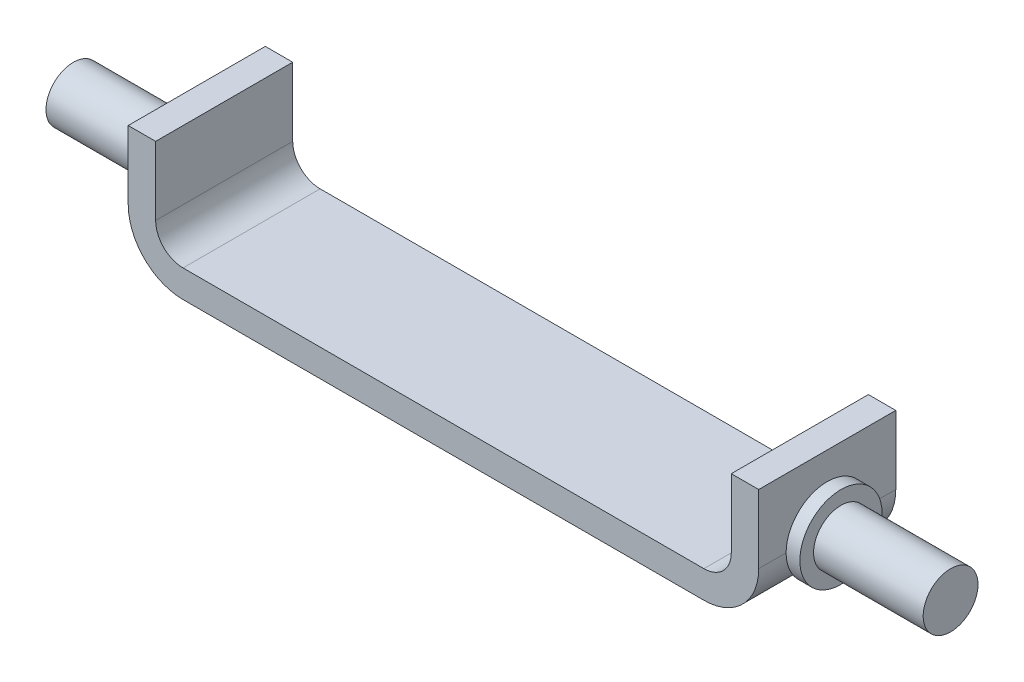
SolidWorks part; units mm, degrees
ref_plane "Front Plane" through (0, 0, 0) normal (0, 0, 1) x (1, 0, 0)
ref_plane "Top Plane" through (0, 0, 0) normal (0, 1, 0) x (1, 0, 0)
ref_plane "Right Plane" through (0, 0, 0) normal (1, 0, 0) x (0, 0, -1)
sketch "Sketch1" plane through (0, 0, 0) normal (0, 0, 1) x (1, 0, 0)
  line L0 (-96.4179, 0) -> (93.5821, 0)
  line L1 (-106.4179, 10) -> (-106.4179, 35)
  line L2 (103.5821, 10) -> (103.5821, 35)
  arc A0 (93.5821, 0) -> (103.5821, 10) centre (93.5821, 10) ccw
  arc A1 (-96.4179, 0) -> (-106.4179, 10) centre (-96.4179, 10) cw
  point P7 (103.5821, 0)
  point P10 (-106.4179, 0)
  dimension "D4" = 10
  dimension "D1" = 210
  dimension "D2" = 35
  dimension "D3" = 35
extrude "Extrude-Thin2" add sketch "Sketch1" along normal blind 50 thin
sketch "Sketch3" plane through (113.5821, 0, 0) normal (1, 0, 0) x (0, 0, -1)
  line L0 (-50, 10) -> (0, 10) construction
  circle A0 centre (-25, 10) radius 10
  dimension "D1" = 20
extrude "Boss-Extrude7" add sketch "Sketch3" along normal blind 45
sketch "Sketch8" plane through (-116.4179, 0, 0) normal (-1, 0, 0) x (0, 0, 1)
  line L0 (50, 10) -> (0, 10) construction
  circle A0 centre (25, 10) radius 10
  dimension "D1" = 20
extrude "Boss-Extrude8" add sketch "Sketch8" along normal blind 45
sketch "Sketch9" plane through (-116.4179, 0, 0) normal (-1, 0, 0) x (0, 0, 1)
  circle A0 centre (25, 10) radius 15
  dimension "D1" = 30
extrude "Boss-Extrude9" add sketch "Sketch9" along normal blind 5
sketch "Sketch10" plane through (113.5821, 0, 0) normal (1, 0, 0) x (0, 0, -1)
  circle A0 centre (-25, 10) radius 15
  dimension "D1" = 30
extrude "Boss-Extrude10" add sketch "Sketch10" along normal blind 5
